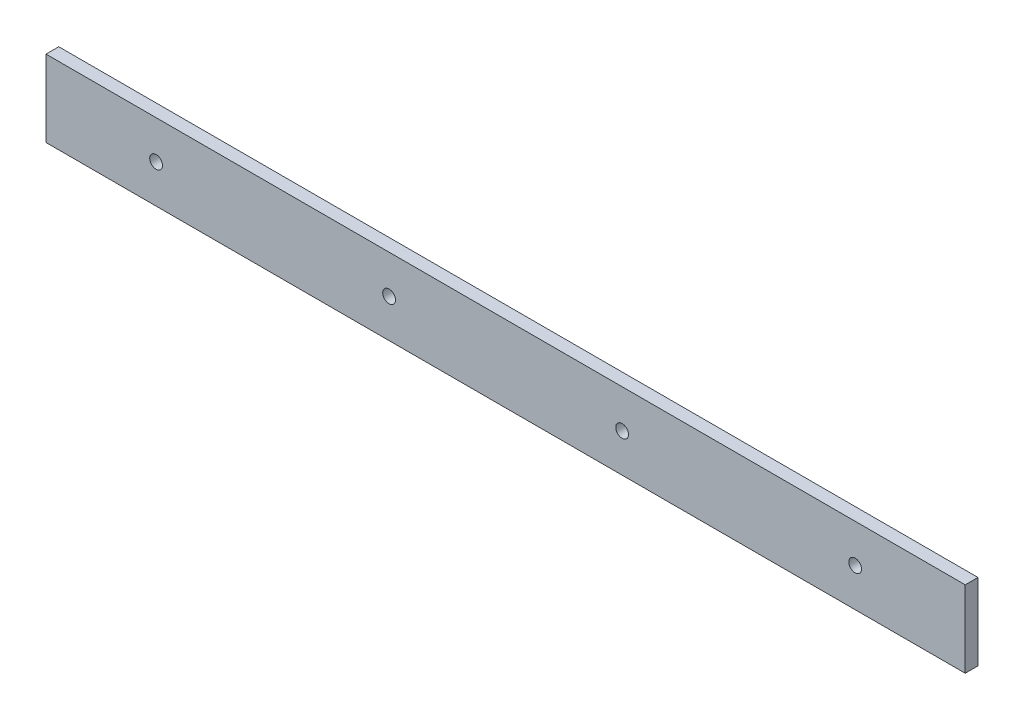
SolidWorks part; units mm, degrees
material "6061-T6 (SS)"
ref_plane "Front Plane" through (0, 0, 0) normal (0, 0, 1) x (1, 0, 0)
ref_plane "Top Plane" through (0, 0, 0) normal (0, 1, 0) x (1, 0, 0)
ref_plane "Right Plane" through (0, 0, 0) normal (1, 0, 0) x (0, 0, -1)
sketch "Sketch1" plane through (0, 0, 0) normal (0, 0, 1) x (1, 0, 0)
  line L0 (0, 19.05) -> (457.2, 19.05) construction
  line L1 (0, 0) -> (457.2, 0)
  line L2 (0, 0) -> (0, 38.1)
  line L3 (0, 38.1) -> (457.2, 38.1)
  line L4 (457.2, 0) -> (457.2, 38.1)
  circle A0 centre (54.7497, 19.05) radius 3.175
  circle A1 centre (170.6499, 19.05) radius 3.175
  circle A2 centre (286.5501, 19.05) radius 3.175
  circle A3 centre (402.4503, 19.05) radius 3.175
  dimension "D3" = 6.35
  dimension "D1" = 457.2
  dimension "D2" = 38.1
  dimension "D5" = 115.9002
  dimension "D6" = 54.7497
  dimension "D4" = 4
extrude "Boss-Extrude1" add sketch "Sketch1" along normal blind 6.35
